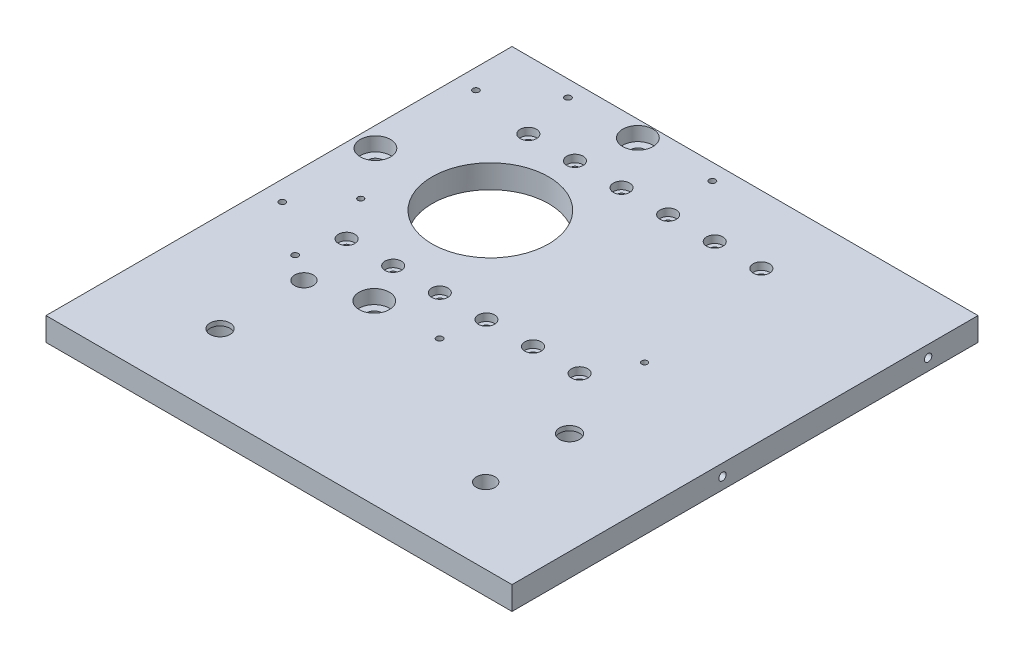
SolidWorks part; units mm, degrees
material "6061-T6 (SS)"
ref_plane "Front" through (0, 0, 0) normal (0, 0, 1) x (1, 0, 0)
ref_plane "Top" through (0, 0, 0) normal (0, 1, 0) x (1, 0, 0)
ref_plane "Right" through (0, 0, 0) normal (1, 0, 0) x (0, 0, -1)
sketch "Sketch1" plane through (0, 0, 0) normal (0, 1, 0) x (1, 0, 0)
  line L1 (-50, -50) -> (50, -50)
  line L2 (-50, -50) -> (-50, 50)
  line L3 (-50, 50) -> (50, 50)
  line L4 (50, -50) -> (50, 50)
  point P0 (0, 0)
  dimension "D1" = 100
  dimension "D2" = 100
extrude "Boss-Extrude1" add sketch "Sketch1" along normal blind 5
hole_wizard "Ø25.0 (25) Diameter Hole1" positions "Sketch2" profile "Sketch3" hole size "Ø25.0" standard "ANSI Metric" end condition up to next
sketch "Sketch2" plane through (0, 5, 0) normal (0, 1, 0) x (1, 0, 0)
  point P0 (-21.8749, 17.2277)
  point P3 (0, 0)
  point P4 (0, 0)
sketch "Sketch3" plane through (-21.8749, 5, -17.2277) normal (1, 0, 0) x (0, 0, 1)
  line L0 (0, 0) -> (0, 5)
  line L1 (0, 5) -> (12.5, 5)
  line L2 (12.5, 5) -> (12.5, 0)
  line L5 (12.5, 0) -> (0, 0)
  line L11 (0, -6.35) -> (0, 107.95) construction
  dimension "Thru Hole Dia." = 25
  dimension "Thru Hole Depth" = 5
hole_wizard "CBORE for M1.6 SHCS1" positions "Sketch4" profile "Sketch5" counterbore size "M1.6" standard "ANSI Metric" end condition up to next
sketch "Sketch4" plane through (0, 5, 0) normal (0, 1, 0) x (1, 0, 0)
  line L1 (50, 50) -> (-50, 50) construction
  line L2 (-50, 50) -> (-50, -50) construction
  point P2 (-32, 35.5049)
  point P9 (-22, 35.5049)
  point P10 (-12, 35.5049)
  point P11 (-2, 35.5049)
  point P12 (8, 35.5049)
  point P13 (18, 35.5049)
  point P24 (18, -3.4951)
  point P25 (8, -3.4951)
  point P26 (-2, -3.4951)
  point P27 (-12, -3.4951)
  point P28 (-22, -3.4951)
  point P29 (-32, -3.4951)
  point P30 (0, 0)
  dimension "D2" = 14.4951
  dimension "D3" = 39
  dimension "D4" = 18
  dimension "D1" = 6
sketch "Sketch5" plane through (-32, 5, -35.5049) normal (1, 0, 0) x (0, 0, 1)
  line L0 (0, 0) -> (0, 5)
  line L1 (0, 5) -> (0.85, 5)
  line L3 (0.85, 5) -> (0.85, 1.6)
  line L4 (0.85, 1.6) -> (1.75, 1.6)
  line L5 (1.75, 1.6) -> (1.75, 0)
  line L7 (1.75, 0) -> (0, 0)
  line L11 (0, -6.35) -> (0, 107.95) construction
  dimension "Thru Hole Dia." = 1.7
  dimension "Thru Hole Depth" = 5
  dimension "C'Bore Dia." = 3.5
  dimension "C'Bore Depth" = 1.6
hole_wizard "M1.6x0.35 Tapped Hole1" positions "Sketch6" profile "Sketch7" tap size "M1.6x0.35" standard "ANSI Metric" end condition up to next
sketch "Sketch6" plane through (0, 0, 0) normal (0, -1, 0) x (-1, 0, 0)
  point P0 (37.9619, 5.5)
  point P1 (-22.9619, 5.5)
sketch "Sketch7" plane through (-37.9619, 0, -5.5) normal (1, 0, 0) x (0, 0, -1)
  line L0 (0, 0) -> (0, 5)
  line L1 (0, 5) -> (0.625, 5)
  line L2 (0.625, 5) -> (0.625, 0)
  line L5 (0.625, 0) -> (0, 0)
  line L11 (0, -6.35) -> (0, 107.95) construction
  dimension "Thru Tap Drill Dia." = 1.25
  dimension "Thru Tap Drill Depth" = 5
cosmetic thread "Hole Thread1"
cosmetic thread "Hole Thread2"
hole_wizard "CBORE for M3 SHCS1" positions "Sketch8" profile "Sketch9" counterbore size "M3" standard "ANSI Metric" end condition up to next
sketch "Sketch8" plane through (0, 5, 0) normal (0, 1, 0) x (1, 0, 0)
  point P0 (-19.5182, 46.5281)
  point P2 (-45.7661, 16.4554)
  point P4 (-17.5083, -12.0463)
sketch "Sketch9" plane through (-19.5182, 5, -46.5281) normal (1, 0, 0) x (0, 0, 1)
  line L0 (0, 0) -> (0, 5)
  line L1 (0, 5) -> (1.6, 5)
  line L3 (1.6, 5) -> (1.6, 3)
  line L4 (1.6, 3) -> (3.25, 3)
  line L5 (3.25, 3) -> (3.25, 0)
  line L7 (3.25, 0) -> (0, 0)
  line L11 (0, -6.35) -> (0, 107.95) construction
  dimension "Thru Hole Dia." = 3.2
  dimension "Thru Hole Depth" = 5
  dimension "C'Bore Dia." = 6.5
  dimension "C'Bore Depth" = 3
hole_wizard "Ø3.0mm Dowel Hole1" positions "Sketch10" profile "Sketch11" hole size "Ø3.0" standard "ANSI Metric"
sketch "Sketch10" plane through (0, 0, 0) normal (0, -1, 0) x (-1, 0, 0)
  point P0 (3.5, -12.04)
  point P2 (34.5, -12.04)
  point P4 (45.75, -3.54)
  point P6 (45.75, 38)
  point P8 (34.5, 46.5)
  point P10 (3.5, 46.5)
sketch "Sketch11" plane through (-3.5, 0, 12.04) normal (1, 0, 0) x (0, 0, -1)
  line L0 (0, 0) -> (0, 5.4013)
  line L1 (0, 5.4013) -> (1.5, 4.5)
  line L2 (1.5, 4.5) -> (1.5, 0)
  line L5 (1.5, 0) -> (0, 0)
  line L10 (0, 5.4013) -> (-1.5, 4.5) construction
  line L11 (0, -6.35) -> (0, 107.95) construction
  dimension "Hole Dia." = 3
  dimension "Hole Depth" = 4.5
  dimension "Drill Angle" = 118
hole_wizard "CBORE for M4 SHCS3" positions "Sketch16" profile "Sketch17" counterbore size "M4" standard "ANSI Metric" end condition up to next
sketch "Sketch16" plane through (0, 0, 0) normal (0, -1, 0) x (-1, 0, 0)
  point P0 (28.877, -33.7768)
  point P2 (-28.1202, -15.7771)
sketch "Sketch17" plane through (-28.877, 0, 33.7768) normal (1, 0, 0) x (0, 0, -1)
  line L0 (0, 0) -> (0, 5)
  line L1 (0, 5) -> (2.15, 5)
  line L3 (2.15, 5) -> (2.15, 4)
  line L4 (2.15, 4) -> (4, 4)
  line L5 (4, 4) -> (4, 0)
  line L7 (4, 0) -> (0, 0)
  line L11 (0, -6.35) -> (0, 107.95) construction
  dimension "Thru Hole Dia." = 4.3
  dimension "Thru Hole Depth" = 5
  dimension "C'Bore Dia." = 8
  dimension "C'Bore Depth" = 4
hole_wizard "Ø4.0mm Dowel Hole1" positions "Sketch18" profile "Sketch19" hole size "Ø4.0" standard "ANSI Metric"
sketch "Sketch18" plane through (0, 5, 0) normal (0, 1, 0) x (1, 0, 0)
  point P0 (-28.8749, -15.7723)
  point P3 (28.1251, -33.7723)
sketch "Sketch19" plane through (-28.8749, 5, 15.7723) normal (1, 0, 0) x (0, 0, 1)
  line L0 (0, 0) -> (0, 4)
  line L1 (0, 4) -> (2, 4)
  line L2 (2, 4) -> (2, 0)
  line L5 (2, 0) -> (0, 0)
  line L10 (0, 4) -> (-2, 4) construction
  line L11 (0, -6.35) -> (0, 107.95) construction
  dimension "Hole Dia." = 4
  dimension "Hole Depth" = 4
  dimension "Drill Angle" = 180
hole_wizard "M2x0.4 Tapped Hole1" positions "Sketch20" profile "Sketch21" tap size "M2x0.4" standard "ANSI Metric"
sketch "Sketch20" plane through (0, 0, -50) normal (0, 0, -1) x (-1, 0, 0)
  point P0 (-27.5563, 2.5)
sketch "Sketch21" plane through (27.5563, 2.5, -50) normal (1, 0, 0) x (0, 1, 0)
  line L0 (0, 0) -> (0, 5.6807)
  line L1 (0, 5.6807) -> (0.8, 5.2)
  line L2 (0.8, 5.2) -> (0.8, 0)
  line L5 (0.8, 0) -> (0, 0)
  line L10 (0, 5.6807) -> (-0.8, 5.2) construction
  line L11 (0, -6.35) -> (0, 107.95) construction
  dimension "Tap Drill Dia." = 1.6
  dimension "Tap Drill Depth" = 5.2
  dimension "Drill Angle" = 118
cosmetic thread "Hole Thread3" parameters "D1"=4, "D2"=2
hole_wizard "M2x0.4 Tapped Hole2" positions "Sketch22" profile "Sketch23" tap size "M2x0.4" standard "ANSI Metric"
sketch "Sketch22" plane through (50, 0, 0) normal (1, 0, 0) x (0, 0, -1)
  point P0 (-4.8329, 2.5)
  point P3 (39.2929, 2.5)
sketch "Sketch23" plane through (50, 2.5, 4.8329) normal (0, 1, 0) x (0, 0, -1)
  line L0 (0, 0) -> (0, 5.6807)
  line L1 (0, 5.6807) -> (0.8, 5.2)
  line L2 (0.8, 5.2) -> (0.8, 0)
  line L5 (0.8, 0) -> (0, 0)
  line L10 (0, 5.6807) -> (-0.8, 5.2) construction
  line L11 (0, -6.35) -> (0, 107.95) construction
  dimension "Tap Drill Dia." = 1.6
  dimension "Tap Drill Depth" = 5.2
  dimension "Drill Angle" = 118
cosmetic thread "Hole Thread4"
cosmetic thread "Hole Thread5"
